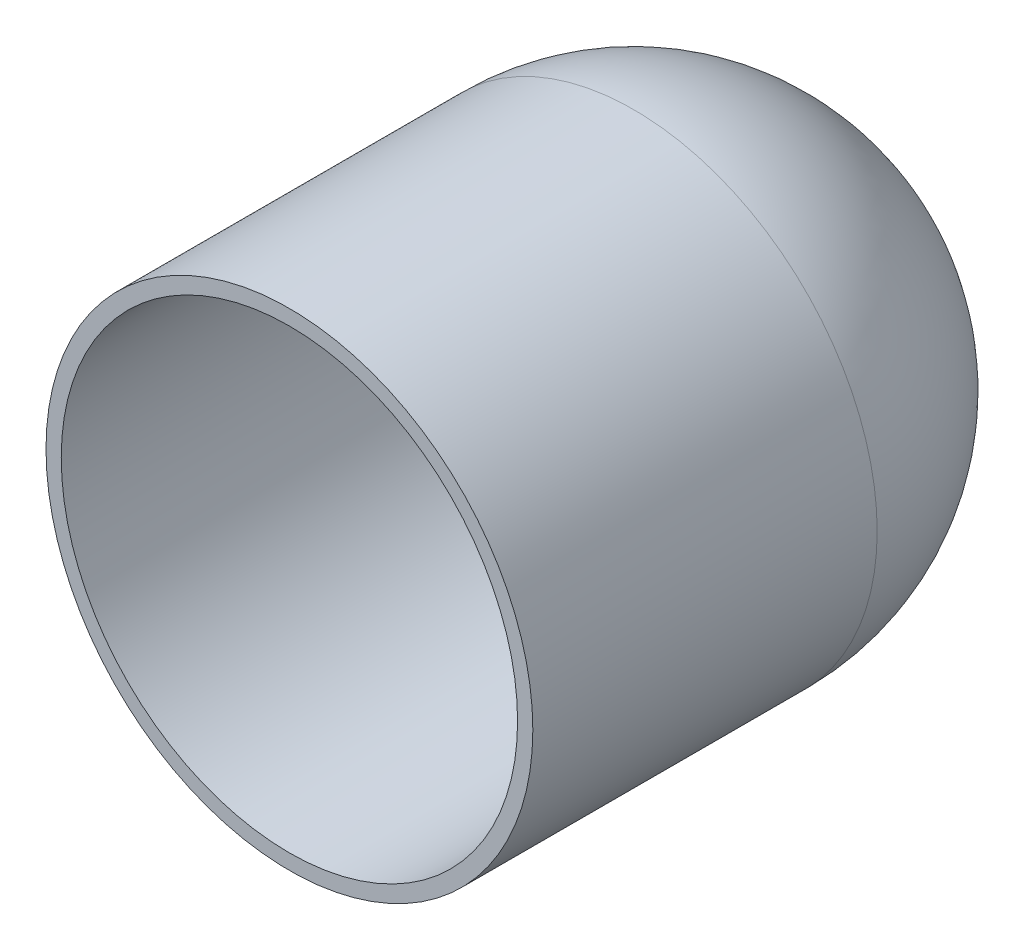
SolidWorks part; units mm, degrees
ref_plane "Front Plane" through (0, 0, 0) normal (0, 0, 1) x (1, 0, 0)
ref_plane "Top Plane" through (0, 0, 0) normal (0, 1, 0) x (1, 0, 0)
ref_plane "Right Plane" through (0, 0, 0) normal (1, 0, 0) x (0, 0, -1)
sketch "Sketch1" plane through (0, 0, 0) normal (0, 0, 1) x (1, 0, 0)
  circle A0 centre (0, 0) radius 22.62
extrude "Boss-Extrude1" add sketch "Sketch1" along normal blind 32
sketch "Sketch2" plane through (0, 0, 0) normal (0, 0, -1) x (-1, 0, 0)
  line L0 (0, 0) -> (0, 22.62)
  line L1 (0, 22.62) -> (0, -22.62)
  line L2 (0, 22.62) -> (0, -22.62)
  circle A0 centre (0, 0) radius 22.62 construction
  circle A1 centre (0, 0) radius 22.62
revolve "Revolve1" add sketch "Sketch2" angle 360 about L0
sketch "Sketch3" plane through (0, 0, 32) normal (0, 0, 1) x (1, 0, 0)
  circle A0 centre (0, 0) radius 5.6731
extrude "Cut-Extrude1" cut sketch "Sketch3" against normal blind 76 contours A0
sketch3d "3DSketch1"
  circle A0 centre (0, 0, -21.897) radius 5.6731 construction
  circle A1 centre (0, 0, -21.897) radius 6.838
  circle A2 centre (0, 0, -21.897) radius 5.6731
  circle A3 centre (0, 0, -21.897) radius 5.6731
  circle A4 centre (0, 0, -21.897) radius 5.6731
  circle A5 centre (0, 0, -21.897) radius 6.838
  point P2 (0, 0, -16.2239)
  point P5 (0, 0, -15.0591)
  point P7 (0, 0, -16.2239)
  point P9 (0, 0, -16.2239)
  point P11 (0, 0, -16.2239)
  point P13 (0, 0, -15.0591)
sketch "Sketch5" plane through (0, 0, 32) normal (0, 0, 1) x (1, 0, 0)
  circle A0 centre (0, 0) radius 21.2037
extrude "Cut-Extrude2" cut sketch "Sketch5" against normal blind 31
sketch "Sketch6" plane through (0, 0, 1) normal (0, 0, 1) x (1, 0, 0)
  line L0 (0, -21.2037) -> (0, 21.2037)
  circle A0 centre (0, 0) radius 21.2037 construction
  circle A1 centre (0, 0) radius 21.2037
